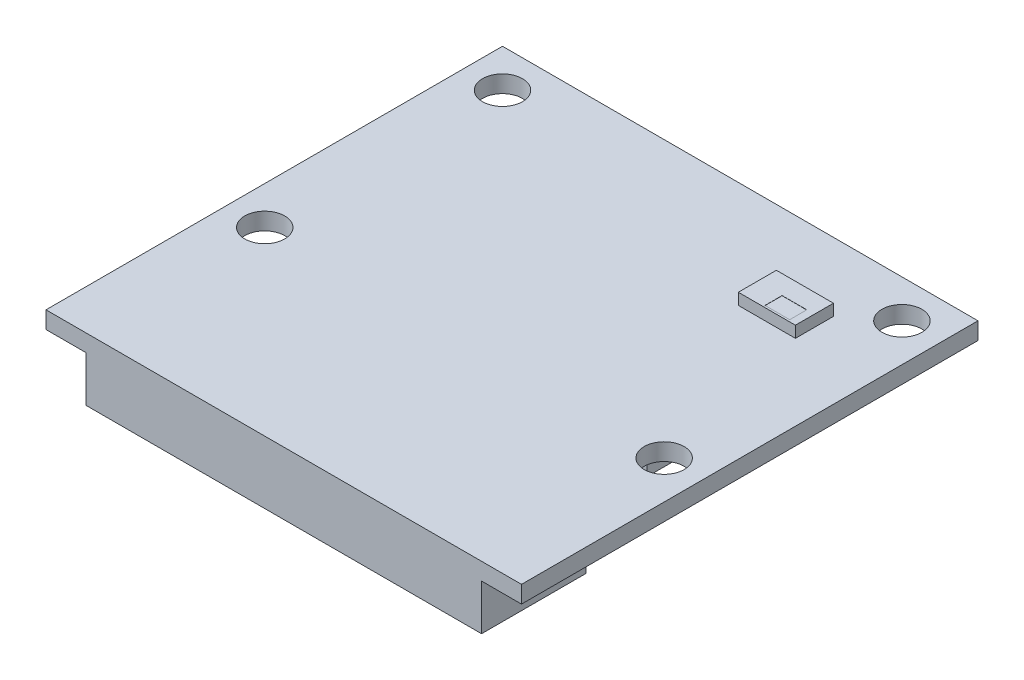
SolidWorks part; units mm, degrees
material "Epoxid, Ungefüllt"
ref_plane "Vorne" through (0, 0, 0) normal (0, 0, 1) x (1, 0, 0)
ref_plane "Oben" through (0, 0, 0) normal (0, 1, 0) x (1, 0, 0)
ref_plane "Rechts" through (0, 0, 0) normal (1, 0, 0) x (0, 0, -1)
sketch "Skizze1" plane through (0, 0, 0) normal (0, 1, 0) x (1, 0, 0)
  line L0 (0, 14.5) -> (0, -9.5) construction
  line L1 (-12.5, 14.5) -> (12.5, 14.5)
  line L2 (-12.5, 14.5) -> (-12.5, -9.5)
  line L3 (-12.5, -9.5) -> (12.5, -9.5)
  line L4 (12.5, 14.5) -> (12.5, -9.5)
  dimension "D1" = 24
  dimension "D2" = 25
  dimension "D3" = 9.5
extrude "PCB" add sketch "Skizze1" against normal blind 0.9
sketch "Skizze2" plane through (0, 0, 0) normal (0, 1, 0) x (1, 0, 0)
  line L0 (12.5, 14.5) -> (-12.5, 14.5) construction
  line L1 (12.5, -9.5) -> (12.5, 14.5) construction
  line L2 (0, 0) -> (0, 9.3158) construction
  circle A0 centre (10.5, 12.5) radius 1.05
  circle A1 centre (10.5, 0) radius 1.05
  circle A2 centre (-10.5, 0) radius 1.05
  circle A3 centre (-10.5, 12.5) radius 1.05
  dimension "D1" = 2.1
  dimension "D2" = 2
  dimension "D3" = 2
  dimension "D4" = 12.5
extrude "Mounting_Holes" cut sketch "Skizze2" against normal through all
sketch "Skizze3" plane through (0, -0.9, 0) normal (0, -1, 0) x (1, 0, 0)
  line L0 (0, 4) -> (0, 0) construction
  line L1 (-10.4, 9.5) -> (10.4, 9.5)
  line L2 (-10.4, 9.5) -> (-10.4, 4)
  line L3 (-10.4, 4) -> (10.4, 4)
  line L4 (10.4, 9.5) -> (10.4, 4)
  line L5 (-12.5, 9.5) -> (12.5, 9.5) construction
  dimension "D1" = 20.8
  dimension "D2" = 5.5
extrude "Connector_closed" add sketch "Skizze3" along normal blind 2.4
sketch "Skizze4" plane through (0, -0.9, 0) normal (0, -1, 0) x (1, 0, 0)
  line L0 (-12.5, -14.5) -> (-12.5, 9.5) construction
  line L1 (-9, -0.9) -> (8.7, -0.9)
  line L2 (-9, -0.9) -> (-9, -12.5)
  line L3 (-9, -12.5) -> (8.7, -12.5)
  line L4 (8.7, -0.9) -> (8.7, -12.5)
  line L5 (12.5, -14.5) -> (-12.5, -14.5) construction
  dimension "D1" = 17.7
  dimension "D2" = 3.5
  dimension "D3" = 2
  dimension "D4" = 13.6
extrude "Components_worst-case_Boundary-Box" add sketch "Skizze4" along normal blind 1.3
sketch "Skizze5" plane through (0, 0, 0) normal (1, 0, 0) x (0, 0, -1)
  line L0 (-9.5, -3.3) -> (-9.5, -0.9) construction
  line L1 (-9.5, 0) -> (14.5, 0) construction
  line L2 (-19.1541, -2.1) -> (0.1541, -2.1) construction
  line L3 (-158.9972, -1.9259) -> (-164.839, -3.2942)
  spline S0 degree 3 poles (-9.5, -2.1) (-29.5972, -2.1) (-48.1056, 0.935) (-88.623, -8.1953) (-134.4443, 3.8252) (-158.9972, -1.9259) knots 0 0 0 0 0.414692 0.514692 1 1 1 1
  dimension "D1" = 2.1
  dimension "D2" = 6
sketch "Skizze6" plane through (0, 0, 9.5) normal (0, 0, 1) x (1, 0, 0)
  line L1 (-8, -2.1) -> (8, -2.1)
  line L2 (-8, -2.1) -> (-8, -2.5)
  line L3 (-8, -2.5) -> (8, -2.5)
  line L4 (8, -2.1) -> (8, -2.5)
  dimension "D1" = 16
  dimension "D2" = 0.4
sweep "Cable_156mm_free_Length" [suppressed] add profiles "Skizze6" path "Skizze5"
sketch "Skizze7" plane through (0, 0, 0) normal (0, 1, 0) x (1, 0, 0)
  line L0 (12.5, 14.5) -> (-12.5, 14.5) construction
  line L1 (5.5, 10.9) -> (8.5, 10.9)
  line L2 (5.5, 10.9) -> (5.5, 8.9)
  line L3 (5.5, 8.9) -> (8.5, 8.9)
  line L4 (8.5, 10.9) -> (8.5, 8.9)
  line L5 (12.5, -9.5) -> (12.5, 14.5) construction
  dimension "D1" = 5.6
  dimension "D2" = 3.6
  dimension "D3" = 4
  dimension "D4" = 7
extrude "Components_worst-case_Boundary-Box2" add sketch "Skizze7" along normal blind 0.6
sketch "Skizze8" plane through (0, 0.6, 0) normal (0, 1, 0) x (1, 0, 0)
  line L0 (12.5, -9.5) -> (12.5, 14.5) construction
  line L1 (8.1, 9) -> (6.8, 9)
  line L2 (8.1, 9) -> (8.1, 9.9)
  line L3 (8.1, 9.9) -> (6.8, 9.9)
  line L4 (6.8, 9) -> (6.8, 9.9)
  line L5 (12.5, 14.5) -> (-12.5, 14.5) construction
  dimension "D1" = 1.3
  dimension "D2" = 0.9
  dimension "D3" = 4.4
  dimension "D4" = 4.6
extrude "Status_LED" cut sketch "Skizze8" against normal blind 0.01
